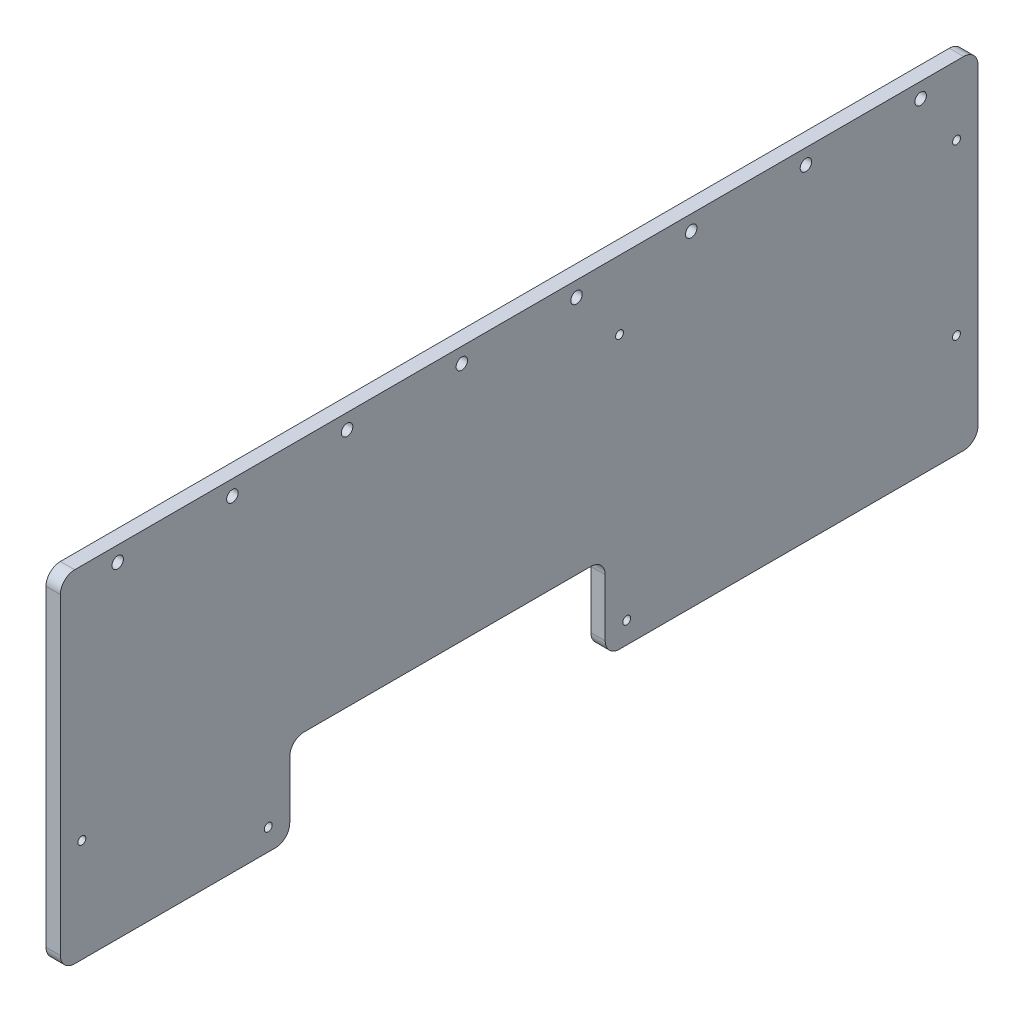
SolidWorks part; units mm, degrees
material "Acrylic (Medium-high impact)"
ref_plane "Front Plane" through (0, 0, 0) normal (0, 0, 1) x (1, 0, 0)
ref_plane "Top Plane" through (0, 0, 0) normal (0, 1, 0) x (1, 0, 0)
ref_plane "Right Plane" through (0, 0, 0) normal (1, 0, 0) x (0, 0, -1)
sketch "Sketch2" plane through (0, 0, 0) normal (1, 0, 0) x (0, 0, -1)
  line L0 (0, 0) -> (0, 294.4501)
  line L1 (0, 294.4501) -> (215.9, 419.1)
  line L2 (215.9, 419.1) -> (431.8, 419.1)
  line L3 (431.8, 419.1) -> (431.8, 0)
  line L4 (431.8, 0) -> (241.3, 0)
  line L5 (241.3, 0) -> (241.3, 38.1)
  line L6 (241.3, 38.1) -> (127, 38.1)
  line L7 (127, 38.1) -> (127, 0)
  line L8 (127, 0) -> (0, 0)
  dimension "D1" = 431.8
  dimension "D2" = 419.1
  dimension "D3" = 127
  dimension "D4" = 114.3
  dimension "D5" = 38.1
  dimension "D6" = 215.9
  dimension "D7" = 150
extrude "Boss-Extrude1" add sketch "Sketch2" along normal blind 6.35 contours L1 L2 L3 L4 L5 L6 L7 L8 L0
sketch "Sketch3" plane through (6.35, 0, 0) normal (1, 0, 0) x (0, 0, -1)
  line L0 (0, 38.1) -> (431.8, 38.1) construction
  line L1 (0, 0) -> (0, 294.4501) construction
  line L2 (431.8, 419.1) -> (431.8, 0) construction
  circle A0 centre (63.5, 38.1) radius 3.9687
  circle A1 centre (368.3, 38.1) radius 3.9688
  dimension "D4" = 7.9375
  dimension "D5" = 7.9375
  dimension "D1" = 38.1
  dimension "D2" = 63.5
  dimension "D3" = 63.5
extrude "Cut-Extrude1" cut sketch "Sketch3" against normal through all
sketch "Sketch4" plane through (6.35, 0, 0) normal (1, 0, 0) x (0, 0, -1)
  line L0 (431.8, 419.1) -> (431.8, 0) construction
  line L1 (215.9, 419.1) -> (431.8, 419.1) construction
  line L2 (393.7, 400.05) -> (393.7, 19.05) construction
  line L4 (393.7, 400.05) -> (330.2, 400.05) construction
  line L5 (330.2, 400.05) -> (330.2, 19.05) construction
  line L6 (330.2, 400.05) -> (330.2, 19.05) construction
  line L7 (330.2, 400.05) -> (323.5506, 19.108) construction
  circle A0 centre (393.7, 400.05) radius 3.175 construction
  circle A1 centre (393.7, 19.05) radius 3.175 construction
  circle A2 centre (323.5506, 19.108) radius 3.175 construction
  circle A3 centre (316.9033, 19.2821) radius 3.175 construction
  circle A4 centre (330.2, 400.05) radius 3.175 construction
  circle A5 centre (330.2, 19.05) radius 3.175 construction
  circle A6 centre (310.26, 19.5721) radius 3.175 construction
  circle A7 centre (303.6228, 19.9781) radius 3.175 construction
  circle A8 centre (296.9937, 20.4998) radius 3.175 construction
  circle A9 centre (290.3747, 21.1372) radius 3.175 construction
  circle A10 centre (283.7678, 21.8899) radius 3.175 construction
  circle A11 centre (277.175, 22.7579) radius 3.175 construction
  circle A12 centre (270.5985, 23.7407) radius 3.175 construction
  dimension "D1" = 6.35
  dimension "D2" = 38.1
  dimension "D3" = 19.05
  dimension "D4" = 381
  dimension "D5" = 10
  dimension "D6" = 1
  dimension "D7" = 101.6
sketch "Sketch5" plane through (6.35, 0, 0) normal (1, 0, 0) x (0, 0, -1)
  line L0 (431.8, 419.1) -> (431.8, 0) construction
  line L1 (431.8, 12.7) -> (425.45, 12.7)
  line L2 (431.8, 12.7) -> (431.8, 25.4)
  line L3 (431.8, 25.4) -> (425.45, 25.4)
  line L4 (425.45, 12.7) -> (425.45, 25.4)
  line L5 (431.8, 0) -> (241.3, 0) construction
  dimension "D1" = 6.35
  dimension "D2" = 12.7
  dimension "D3" = 12.7
extrude "Cut-Extrude3" cut sketch "Sketch5" against normal through all
pattern_linear "LPattern1" count 16 spacing 25.4 along (0, 1, 0) of "Cut-Extrude3"
sketch "Sketch6" plane through (6.35, 0, 0) normal (1, 0, 0) x (0, 0, -1)
  line L0 (0, 0) -> (0, 294.4501) construction
  line L1 (0, 12.7) -> (6.35, 12.7)
  line L2 (0, 12.7) -> (0, 25.4)
  line L3 (0, 25.4) -> (6.35, 25.4)
  line L4 (6.35, 12.7) -> (6.35, 25.4)
  line L5 (425.45, 12.7) -> (431.8, 12.7) construction
  line L6 (425.45, 25.4) -> (425.45, 12.7) construction
  line L7 (127, 0) -> (0, 0) construction
  dimension "D1" = 12.7
extrude "Cut-Extrude4" cut sketch "Sketch6" against normal through all
pattern_linear "LPattern2" count 11 spacing 25.4 along (0, 1, 0) of "Cut-Extrude4"
sketch "Sketch7" plane through (6.35, 0, 0) normal (1, 0, 0) x (0, 0, -1)
  line L0 (127, 38.1) -> (127, 0) construction
  line L1 (127, 12.7) -> (120.65, 12.7)
  line L2 (127, 12.7) -> (127, 25.4)
  line L3 (127, 25.4) -> (120.65, 25.4)
  line L4 (120.65, 12.7) -> (120.65, 25.4)
  line L5 (241.3, 38.1) -> (127, 38.1) construction
  line L6 (127, 38.1) -> (139.7, 38.1)
  line L7 (127, 38.1) -> (127, 44.45)
  line L8 (127, 44.45) -> (139.7, 44.45)
  line L9 (139.7, 38.1) -> (139.7, 44.45)
  line L10 (241.3, 0) -> (241.3, 38.1) construction
  line L11 (152.4, 38.1) -> (165.1, 38.1)
  line L12 (152.4, 38.1) -> (152.4, 44.45)
  line L13 (152.4, 44.45) -> (165.1, 44.45)
  line L14 (165.1, 38.1) -> (165.1, 44.45)
  line L15 (177.8, 38.1) -> (190.5, 38.1)
  line L16 (177.8, 38.1) -> (177.8, 44.45)
  line L17 (177.8, 44.45) -> (190.5, 44.45)
  line L18 (190.5, 38.1) -> (190.5, 44.45)
  line L19 (241.3, 25.4) -> (247.65, 25.4)
  line L20 (241.3, 25.4) -> (241.3, 12.7)
  line L21 (241.3, 12.7) -> (247.65, 12.7)
  line L22 (247.65, 25.4) -> (247.65, 12.7)
  line L23 (0, 12.7) -> (6.35, 12.7) construction
  line L24 (6.35, 12.7) -> (6.35, 25.4) construction
  line L25 (127, 0) -> (0, 0) construction
  line L26 (431.8, 0) -> (241.3, 0) construction
  line L27 (203.2, 44.45) -> (215.9, 44.45)
  line L28 (203.2, 44.45) -> (203.2, 38.1)
  line L29 (203.2, 38.1) -> (215.9, 38.1)
  line L30 (215.9, 44.45) -> (215.9, 38.1)
  line L32 (241.3, 38.1) -> (228.6, 38.1)
  line L33 (241.3, 38.1) -> (241.3, 44.45)
  line L34 (241.3, 44.45) -> (228.6, 44.45)
  line L35 (228.6, 38.1) -> (228.6, 44.45)
  dimension "D1" = 12.7
  dimension "D2" = 12.7
  dimension "D4" = 12.7
  dimension "D5" = 12.7
  dimension "D6" = 12.7
extrude "Cut-Extrude5" cut sketch "Sketch7" against normal through all
sketch "Sketch8" plane through (6.35, 0, 0) normal (1, 0, 0) x (0, 0, -1)
  line L0 (201.9351, 411.0373) -> (212.9336, 417.3873)
  line L1 (201.9351, 411.0373) -> (205.1101, 405.5381)
  line L2 (212.9336, 417.3873) -> (216.1086, 411.8881)
  line L3 (205.1101, 405.5381) -> (216.1086, 411.8881)
  line L4 (0, 294.4501) -> (215.9, 419.1) construction
  line L5 (6.35, 279.4) -> (0, 279.4) construction
  line L6 (6.35, 266.7) -> (6.35, 279.4) construction
  line L7 (216.1086, 411.8881) -> (7.1367, 291.2381) construction
  line L8 (6.35, 279.4) -> (6.35, 292.1) construction
  line L9 (215.9, 412.75) -> (215.6832, 412.6248) construction
  line L10 (7.1367, 291.2381) -> (3.9617, 296.7373) construction
  line L11 (6.35, 292.1) -> (6.5668, 292.2252) construction
  line L12 (215.9, 419.1) -> (215.9, 412.75) construction
  line L13 (215.9, 419.1) -> (431.8, 419.1) construction
  dimension "D1" = 215.9
  dimension "D2" = 241.3
  dimension "D3" = 6.35
extrude "Cut-Extrude6" cut sketch "Sketch8" against normal through all
pattern_linear "LPattern3" count 10 spacing 25.4 along (0, -0.5, 0.866) of "Cut-Extrude6"
sketch "Sketch9" plane through (6.35, 0, 0) normal (1, 0, 0) x (0, 0, -1)
  line L0 (215.9, 419.1) -> (431.8, 419.1) construction
  line L1 (419.1, 419.1) -> (406.4, 419.1)
  line L2 (419.1, 419.1) -> (419.1, 412.75)
  line L3 (419.1, 412.75) -> (406.4, 412.75)
  line L4 (406.4, 419.1) -> (406.4, 412.75)
  line L5 (431.8, 406.4) -> (425.45, 406.4) construction
  line L6 (425.45, 406.4) -> (425.45, 393.7) construction
  line L7 (431.8, 419.1) -> (431.8, 406.4) construction
  dimension "D1" = 12.7
extrude "Cut-Extrude7" cut sketch "Sketch9" against normal through all
pattern_linear "LPattern4" count 8 spacing 25.4 along (0, 0, 1) of "Cut-Extrude7"
sketch "Sketch10" plane through (6.35, 0, 0) normal (1, 0, 0) x (0, 0, -1)
  line L0 (127, 0) -> (0, 0) construction
  line L1 (146.05, 273.05) -> (222.25, 273.05) construction
  line L2 (146.05, 273.05) -> (146.05, 57.15) construction
  line L3 (146.05, 57.15) -> (222.25, 57.15) construction
  line L4 (222.25, 273.05) -> (222.25, 57.15) construction
  line L5 (146.05, 273.05) -> (19.05, 273.05) construction
  line L6 (146.05, 273.05) -> (146.05, 247.65) construction
  line L7 (146.05, 247.65) -> (19.05, 247.65) construction
  line L8 (19.05, 273.05) -> (19.05, 247.65) construction
  line L9 (0, 254) -> (0, 266.7) construction
  line L10 (127, 44.45) -> (127, 25.4) construction
  line L11 (241.3, 25.4) -> (241.3, 44.45) construction
  line L12 (152.4, 38.1) -> (139.7, 38.1) construction
  circle A0 centre (222.25, 273.05) radius 3.175
  circle A1 centre (222.25, 57.15) radius 3.175
  circle A2 centre (146.05, 57.15) radius 3.175
  circle A3 centre (146.05, 273.05) radius 3.175
  circle A4 centre (19.05, 273.05) radius 3.175 construction
  circle A5 centre (19.05, 247.65) radius 3.175 construction
  circle A6 centre (146.05, 247.65) radius 3.175 construction
  dimension "D4" = 6.35
  dimension "D1" = 273.05
  dimension "D2" = 19.05
  dimension "D3" = 247.65
  dimension "D5" = 19.05
  dimension "D6" = 19.05
  dimension "D7" = 19.05
extrude "Cut-Extrude8" cut sketch "Sketch10" against normal through all
sketch "Sketch11" plane through (6.35, 0, 0) normal (1, 0, 0) x (0, 0, -1)
  line L0 (127, 0) -> (0, 0) construction
  line L1 (0, 254) -> (0, 266.7) construction
  line L5 (241.3, 0) -> (241.3, 12.7) construction
  line L6 (177.8, 38.1) -> (165.1, 38.1) construction
  line L7 (38.1, 260.35) -> (266.7, 260.35) construction
  line L8 (266.7, 260.35) -> (266.7, 63.5) construction
  circle A0 centre (38.1, 260.35) radius 3.9688
  circle A1 centre (266.7, 63.5) radius 3.9688 construction
  circle A2 centre (266.7, 260.35) radius 3.9688
  dimension "D3" = 7.9375
  dimension "D1" = 260.35
  dimension "D2" = 38.1
  dimension "D4" = 25.4
  dimension "D5" = 25.4
extrude "Cut-Extrude9" cut sketch "Sketch11" against normal through all
sketch "Sketch12" plane through (6.35, 0, 0) normal (1, 0, 0) x (0, 0, -1)
  line L0 (127, 50.8) -> (127, 38.1)
  line L1 (120.65, 25.4) -> (127, 25.4)
  line L2 (120.65, 25.4) -> (120.65, 12.7)
  line L3 (120.65, 12.7) -> (127, 12.7)
  line L4 (127, 25.4) -> (127, 12.7)
  line L5 (120.65, 50.8) -> (127, 50.8)
  line L6 (120.65, 50.8) -> (120.65, 38.1)
  line L7 (120.65, 38.1) -> (127, 38.1)
  line L8 (127, 76.2) -> (127, 63.5)
  line L9 (120.65, 76.2) -> (127, 76.2)
  line L10 (120.65, 76.2) -> (120.65, 63.5)
  line L11 (120.65, 63.5) -> (127, 63.5)
  line L12 (127, 101.6) -> (127, 88.9)
  line L13 (120.65, 101.6) -> (127, 101.6)
  line L14 (120.65, 101.6) -> (120.65, 88.9)
  line L15 (120.65, 88.9) -> (127, 88.9)
  line L16 (127, 127) -> (127, 114.3)
  line L17 (120.65, 127) -> (127, 127)
  line L18 (120.65, 127) -> (120.65, 114.3)
  line L19 (120.65, 114.3) -> (127, 114.3)
  line L20 (127, 152.4) -> (127, 139.7) construction
  line L21 (120.65, 152.4) -> (127, 152.4) construction
  line L22 (120.65, 152.4) -> (120.65, 139.7) construction
  line L23 (120.65, 139.7) -> (127, 139.7) construction
  line L24 (127, 177.8) -> (127, 165.1) construction
  line L25 (120.65, 177.8) -> (127, 177.8) construction
  line L26 (120.65, 177.8) -> (120.65, 165.1) construction
  line L27 (120.65, 165.1) -> (127, 165.1) construction
  dimension "D1" = 7
extrude "Cut-Extrude13" cut sketch "Sketch12" against normal through all
sketch "Sketch13" plane through (6.35, 0, 0) normal (1, 0, 0) x (0, 0, -1)
  line L1 (120.65, 25.4) -> (120.65, 12.7) construction
  line L2 (84.65, 117.2) -> (347.15, 117.2) construction
  line L3 (84.65, 117.2) -> (6.35, 117.2) construction
  line L4 (6.35, 114.3) -> (6.35, 127) construction
  line L5 (347.15, 117.2) -> (425.45, 117.2) construction
  line L6 (425.45, 127) -> (425.45, 114.3) construction
  circle A0 centre (84.65, 117.2) radius 20
  circle A1 centre (347.15, 117.2) radius 20
  dimension "D2" = 40
  dimension "D1" = 9.8
  dimension "D3" = 36
sketch "Sketch14" plane through (6.35, 0, 0) normal (1, 0, 0) x (0, 0, -1)
  line L0 (36.9572, 315.7873) -> (47.9558, 322.1373)
  line L1 (36.9572, 315.7873) -> (40.1322, 310.2881)
  line L2 (47.9558, 322.1373) -> (51.1308, 316.6381)
  line L3 (40.1322, 310.2881) -> (51.1308, 316.6381)
  line L4 (80.9513, 341.1873) -> (91.9498, 347.5373)
  line L5 (80.9513, 341.1873) -> (84.1263, 335.6881)
  line L6 (91.9498, 347.5373) -> (95.1248, 342.0381)
  line L7 (84.1263, 335.6881) -> (95.1248, 342.0381)
  line L8 (91.9498, 347.5373) -> (95.1248, 342.0381) construction
extrude "Cut-Extrude15" cut sketch "Sketch14" against normal through all
sketch "Sketch15" plane through (6.35, 0, 0) normal (1, 0, 0) x (0, 0, -1)
  line L0 (43.8866, 319.2853) -> (85.4558, 343.2853) construction
  line L1 (46.8439, 314.1631) -> (53.1939, 303.1646) construction
  line L3 (64.6712, 331.2853) -> (64.4535, 331.6623) construction
  line L4 (58.9543, 328.4873) -> (69.9528, 334.8373) construction
  line L5 (29.1337, 303.9381) -> (62.1293, 322.9881) construction
  line L6 (31.5586, 305.3381) -> (62.1293, 322.9881)
  line L7 (73.1278, 329.3381) -> (103.6985, 346.9881)
  line L8 (73.1278, 329.3381) -> (106.1234, 348.3881) construction
  circle A0 centre (43.8866, 319.2853) radius 18.6147
  circle A1 centre (85.4558, 343.2853) radius 18.6147
  dimension "D2" = 12.7
  dimension "D1" = 48
extrude "Cut-Extrude16" cut sketch "Sketch15" against normal through all contours L6 A0 | L7 A1
sketch "Sketch17" plane through (6.35, 0, 0) normal (1, 0, 0) x (0, 0, -1)
  line L0 (0, 139.7) -> (6.35, 139.7) construction
  line L1 (19.05, 146.05) -> (31.75, 146.05)
  line L2 (19.05, 146.05) -> (19.05, 139.7)
  line L3 (19.05, 139.7) -> (31.75, 139.7)
  line L4 (31.75, 146.05) -> (31.75, 139.7)
  line L5 (6.35, 139.7) -> (6.35, 152.4) construction
  dimension "D1" = 12.7
  dimension "D2" = 6.35
  dimension "D3" = 12.7
extrude "Cut-Extrude17" cut sketch "Sketch17" against normal through all
pattern_linear "LPattern5" count 17 spacing 25.4 along (0, 0, -1) of "Cut-Extrude17"
pattern_linear "LPattern6" count 2 spacing 120.65 along (0, 0, -1) of "Cut-Extrude13"
sketch "Sketch18" plane through (6.35, 0, 0) normal (1, 0, 0) x (0, 0, -1)
  line L1 (127, 120.65) -> (139.7, 120.65)
  line L2 (127, 120.65) -> (127, 114.3)
  line L3 (127, 114.3) -> (139.7, 114.3)
  line L4 (139.7, 120.65) -> (139.7, 114.3)
  dimension "D1" = 12.7
  dimension "D2" = 6.35
extrude "Cut-Extrude18" cut sketch "Sketch18" against normal through all
pattern_linear "LPattern7" count 5 spacing 25.4 along (0, 0, -1) of "Cut-Extrude18"
sketch "Sketch19" plane through (6.35, 0, 0) normal (1, 0, 0) x (0, 0, -1)
  line L0 (25.4, 279.7854) -> (222.7059, 393.7)
  line L1 (222.7059, 393.7) -> (406.4, 393.7)
  line L2 (406.4, 393.7) -> (406.4, 165.1)
  line L3 (406.4, 165.1) -> (25.4, 165.1)
  line L4 (25.4, 165.1) -> (25.4, 279.7854)
  line L5 (0, 228.6) -> (0, 241.3) construction
  line L6 (431.8, 292.1) -> (431.8, 279.4) construction
  line L7 (368.3, 419.1) -> (381, 419.1) construction
  line L9 (146.9425, 379.2873) -> (157.941, 385.6373) construction
  line L10 (124.9454, 366.5873) -> (135.9439, 372.9373) construction
  line L11 (222.25, 139.7) -> (234.95, 139.7) construction
  point P16 (130.4447, 369.7623)
  dimension "D1" = 25.4
  dimension "D2" = 25.4
  dimension "D3" = 25.4
  dimension "D4" = 25.4
  dimension "D5" = 25.4
extrude "Cut-Extrude19" cut sketch "Sketch19" against normal through all
sketch "Sketch20" plane through (6.35, 0, 0) normal (1, 0, 0) x (0, 0, -1)
  line L0 (165.1, 120.65) -> (152.4, 120.65) construction
  line L1 (133.35, 107.95) -> (234.95, 107.95)
  line L2 (133.35, 107.95) -> (133.35, 50.8)
  line L3 (133.35, 50.8) -> (234.95, 50.8)
  line L4 (234.95, 107.95) -> (234.95, 50.8)
  line L5 (120.65, 101.6) -> (120.65, 88.9) construction
  line L6 (177.8, 38.1) -> (165.1, 38.1) construction
  line L7 (247.65, 101.6) -> (247.65, 88.9) construction
  dimension "D1" = 12.7
  dimension "D2" = 12.7
  dimension "D3" = 12.7
  dimension "D4" = 12.7
extrude "Cut-Extrude20" cut sketch "Sketch20" against normal through all
sketch "Sketch21" plane through (6.35, 0, 0) normal (1, 0, 0) x (0, 0, -1)
  line L0 (266.7, 25.4) -> (308.203, 25.4)
  line L1 (25.4, 133.35) -> (25.4, 82.0941)
  line L2 (308.203, 25.4) -> (406.4, 82.0941)
  line L3 (25.4, 82.0941) -> (101.6, 38.1)
  line L4 (406.4, 82.0941) -> (406.4, 133.35)
  line L5 (406.4, 133.35) -> (266.7, 133.35)
  line L6 (266.7, 133.35) -> (266.7, 25.4)
  line L7 (406.4, 165.1) -> (406.4, 393.7) construction
  line L8 (431.8, 0) -> (241.3, 0) construction
  line L9 (241.3, 25.4) -> (241.3, 38.1) construction
  line L10 (387.35, 146.05) -> (374.65, 146.05) construction
  line L11 (101.6, 38.1) -> (101.6, 133.35)
  line L12 (101.6, 133.35) -> (25.4, 133.35)
  line L13 (0, 101.6) -> (0, 114.3) construction
  line L14 (127, 101.6) -> (127, 88.9) construction
  line L20 (25.4, 38.1) -> (25.4, 25.4)
  line L21 (25.4, 25.4) -> (47.397, 25.4)
  line L22 (47.397, 25.4) -> (25.4, 38.1)
  circle A0 centre (63.5, 38.1) radius 3.9687 construction
  circle A1 centre (368.3, 38.1) radius 3.9688 construction
  dimension "D4" = 150
  dimension "D5" = 19.05
  dimension "D9" = 19.05
  dimension "D1" = 25.4
  dimension "D2" = 25.4
  dimension "D3" = 12.7
  dimension "D6" = 25.4
  dimension "D7" = 25.4
  dimension "D8" = 120
  dimension "D12" = 19.05
extrude "Cut-Extrude21" cut sketch "Sketch21" against normal through all
sketch "Sketch22" plane through (6.35, 0, 0) normal (1, 0, 0) x (0, 0, -1)
  line L0 (384.403, 25.4) -> (406.4, 38.1)
  line L1 (406.4, 38.1) -> (406.4, 25.4)
  line L2 (406.4, 25.4) -> (384.403, 25.4)
  line L3 (406.4, 82.0941) -> (406.4, 133.35) construction
  line L4 (266.7, 25.4) -> (308.203, 25.4) construction
  line L5 (358.775, 54.5978) -> (377.825, 21.6022) construction
  line L6 (308.203, 25.4) -> (406.4, 82.0941) construction
  point P11 (368.3, 38.1)
extrude "Cut-Extrude22" cut sketch "Sketch22" against normal through all
sketch "Sketch26" plane through (6.35, 0, 0) normal (1, 0, 0) x (0, 0, -1)
  line L0 (278.9441, 133.35) -> (234.95, 107.95) construction
  line L1 (278.9441, 133.35) -> (275.7691, 138.8493) construction
  line L2 (234.95, 107.95) -> (231.775, 113.4493) construction
  line L3 (275.7691, 138.8493) -> (231.775, 113.4493) construction
  line L4 (406.4, 133.35) -> (266.7, 133.35) construction
  line L5 (228.6, 120.65) -> (228.6, 114.3) construction
  line L6 (308.203, 25.4) -> (406.4, 82.0941) construction
  line L7 (266.7, 133.35) -> (266.7, 126.2809)
  line L8 (266.7, 133.35) -> (266.7, 25.4) construction
  line L9 (266.7, 126.2809) -> (278.9441, 133.35)
  line L10 (278.9441, 133.35) -> (266.7, 133.35)
  line L11 (89.3559, 133.35) -> (101.6, 126.2809)
  line L12 (101.6, 133.35) -> (25.4, 133.35) construction
  line L13 (101.6, 38.1) -> (101.6, 133.35) construction
  line L14 (101.6, 126.2809) -> (101.6, 133.35)
  line L15 (101.6, 133.35) -> (89.3559, 133.35)
  line L16 (25.4, 82.0941) -> (101.6, 38.1) construction
  line L17 (266.7, 32.4691) -> (278.9441, 25.4)
  line L18 (266.7, 133.35) -> (266.7, 25.4) construction
  line L19 (266.7, 25.4) -> (308.203, 25.4) construction
  line L20 (278.9441, 25.4) -> (266.7, 25.4)
  line L21 (266.7, 25.4) -> (266.7, 32.4691)
  line L22 (133.35, 107.95) -> (133.35, 100.8809)
  line L23 (133.35, 107.95) -> (133.35, 50.8) construction
  line L24 (133.35, 100.8809) -> (145.5941, 107.95)
  line L25 (234.95, 107.95) -> (133.35, 107.95) construction
  line L26 (145.5941, 107.95) -> (133.35, 107.95)
  line L27 (234.95, 107.95) -> (222.7059, 107.95)
  line L28 (222.7059, 107.95) -> (234.95, 100.8809)
  line L29 (234.95, 50.8) -> (234.95, 107.95) construction
  line L30 (234.95, 100.8809) -> (234.95, 107.95)
  line L31 (133.35, 50.8) -> (145.5941, 50.8)
  line L32 (133.35, 50.8) -> (234.95, 50.8) construction
  line L33 (145.5941, 50.8) -> (133.35, 57.8691)
  line L34 (133.35, 57.8691) -> (133.35, 50.8)
  line L35 (234.95, 50.8) -> (222.7059, 50.8)
  line L36 (222.7059, 50.8) -> (234.95, 57.8691)
  line L37 (234.95, 57.8691) -> (234.95, 50.8)
extrude "Boss-Extrude4" add sketch "Sketch26" against normal through all
sketch "Sketch27" plane through (6.35, 0, 0) normal (1, 0, 0) x (0, 0, -1)
  line L0 (12.7, 163.83) -> (12.7, 12.7)
  line L1 (12.7, 12.7) -> (114.3, 12.7)
  line L2 (114.3, 12.7) -> (114.3, 50.8)
  line L3 (114.3, 50.8) -> (254, 50.8)
  line L4 (254, 50.8) -> (254, 12.7)
  line L5 (254, 12.7) -> (419.1, 12.7)
  line L6 (419.1, 12.7) -> (419.1, 163.83)
  line L7 (419.1, 163.83) -> (12.7, 163.83)
  line L8 (0, 101.6) -> (0, 114.3) construction
  line L9 (127, 0) -> (0, 0) construction
  line L10 (127, 38.1) -> (127, 25.4) construction
  line L11 (177.8, 38.1) -> (165.1, 38.1) construction
  line L12 (241.3, 25.4) -> (241.3, 38.1) construction
  line L13 (431.8, 0) -> (241.3, 0) construction
  line L14 (431.8, 63.5) -> (431.8, 50.8) construction
  line L15 (31.75, 146.05) -> (19.05, 146.05) construction
  point P12 (127, 31.75)
  dimension "D1" = 12.7
  dimension "D2" = 12.7
  dimension "D3" = 12.7
  dimension "D4" = 12.7
  dimension "D5" = 12.7
  dimension "D6" = 12.7
  dimension "D7" = 12.7
  dimension "D8" = 17.78
extrude "Boss-Extrude5" add sketch "Sketch27" against normal blind 6.35 separate body
sketch "Sketch29" plane through (6.35, 0, 0) normal (1, 0, 0) x (0, 0, -1)
  line L0 (12.7, 157.1625) -> (419.1, 157.1625) construction
  line L1 (12.7, 163.83) -> (12.7, 12.7) construction
  line L2 (419.1, 12.7) -> (419.1, 163.83) construction
  line L4 (25.4, 165.1) -> (406.4, 165.1) construction
  circle A0 centre (38.1, 157.1625) radius 2.54
  circle A2 centre (88.9, 157.1625) radius 2.54
  circle A4 centre (139.7, 157.1625) radius 2.54
  circle A6 centre (190.5, 157.1625) radius 2.54
  circle A8 centre (241.3, 157.1625) radius 2.54
  circle A10 centre (292.1, 157.1625) radius 2.54
  circle A12 centre (342.9, 157.1625) radius 2.54
  circle A14 centre (393.7, 157.1625) radius 2.54
  circle A16 centre (63.5, 157.1625) radius 2.54 [skipped]
  circle A17 centre (114.3, 157.1625) radius 2.54 [skipped]
  circle A18 centre (165.1, 157.1625) radius 2.54 [skipped]
  circle A19 centre (215.9, 157.1625) radius 2.54 [skipped]
  circle A20 centre (266.7, 157.1625) radius 2.54 [skipped]
  circle A21 centre (317.5, 157.1625) radius 2.54 [skipped]
  circle A22 centre (368.3, 157.1625) radius 2.54 [skipped]
  circle A23 centre (419.1, 157.1625) radius 2.54 [skipped]
  dimension "D3" = 5.08
  dimension "D1" = 7.9375
  dimension "D2" = 25.4
  dimension "D4" = 16
extrude "Cut-Extrude23" cut sketch "Sketch29" against normal through all
sketch "Sketch30" plane through (6.35, 0, 0) normal (1, 0, 0) x (0, 0, -1)
  line L0 (12.7, 12.7) -> (114.3, 12.7) construction
  line L1 (12.7, 163.83) -> (12.7, 12.7) construction
  line L2 (254, 12.7) -> (419.1, 12.7) construction
  line L3 (419.1, 12.7) -> (419.1, 163.83) construction
  line L4 (254, 50.8) -> (254, 12.7) construction
  line L5 (114.3, 12.7) -> (114.3, 50.8) construction
  circle A0 centre (22.225, 58.42) radius 1.75
  circle A1 centre (104.775, 22.225) radius 1.75
  circle A2 centre (263.525, 22.225) radius 1.75
  circle A3 centre (409.575, 58.42) radius 1.75
  dimension "D9" = 3.5
  dimension "D1" = 45.72
  dimension "D2" = 9.525
  dimension "D3" = 9.525
  dimension "D4" = 9.525
  dimension "D5" = 45.72
  dimension "D6" = 9.525
  dimension "D7" = 9.525
  dimension "D8" = 9.525
extrude "Cut-Extrude24" cut sketch "Sketch30" against normal through all
sketch "Sketch31" plane through (6.35, 0, 0) normal (1, 0, 0) x (0, 0, -1)
  line L1 (266.7, 126.2809) -> (266.7, 32.4691) construction
  line L2 (406.4, 133.35) -> (278.9441, 133.35) construction
  line L4 (431.8, 139.7) -> (431.8, 127) construction
  circle A0 centre (260.35, 133.35) radius 1.75
  circle A1 centre (409.575, 133.35) radius 1.75
  dimension "D1" = 3.5
  dimension "D2" = 22.225
  dimension "D3" = 6.35
  dimension "D4" = 0
extrude "Cut-Extrude25" cut sketch "Sketch31" against normal through all
delete or keep bodies "Body-Delete1" type delete bodies bodies 130
fillet "Fillet2" radius 6.35 8 edges at (3.175, 163.83, -12.7) (3.175, 163.83, -419.1) (3.175, 12.7, -419.1) (3.175, 50.8, -254) (3.175, 12.7, -254) (3.175, 50.8, -114.3) (3.175, 12.7, -114.3) (3.175, 12.7, -12.7)
